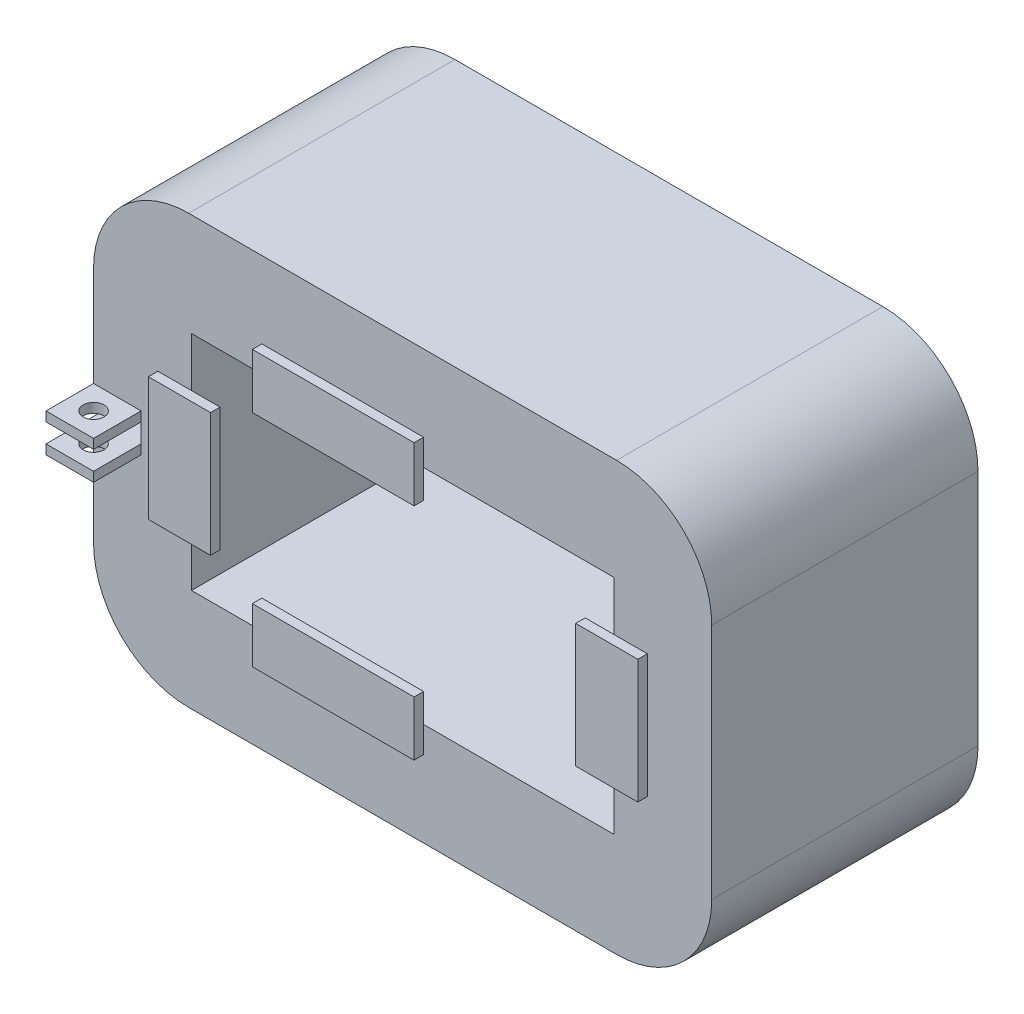
SolidWorks part; units mm, degrees
ref_plane "前基準面" through (0, 0, 0) normal (0, 0, 1) x (1, 0, 0)
ref_plane "上基準面" through (0, 0, 0) normal (0, 1, 0) x (1, 0, 0)
ref_plane "右基準面" through (0, 0, 0) normal (1, 0, 0) x (0, 0, -1)
sketch "草圖1" plane through (0, 0, 0) normal (0, 0, 1) x (1, 0, 0)
  line L0 (-9.02, 0) -> (7.9922, 0) construction
  line L2 (-59.9347, 22.5) -> (5.0653, 22.5)
  line L3 (-59.9347, 22.5) -> (-59.9347, -22.5)
  line L4 (-59.9347, -22.5) -> (5.0653, -22.5)
  line L5 (5.0653, 22.5) -> (5.0653, -22.5)
  dimension "D1" = 45
  dimension "D2" = 22.5
  dimension "D3" = 65
extrude "填料-伸長1" add sketch "草圖1" along normal blind 28
sketch "草圖2" plane through (0, 0, 0) normal (0, 0, 1) x (1, 0, 0)
  line L0 (-59.9347, 0) -> (5.361, 0) construction
  line L1 (-59.9347, 22.5) -> (-59.9347, -22.5) construction
  line L2 (-27.4347, 22.5) -> (-27.4347, -22.5) construction
  line L3 (5.0653, 22.5) -> (-59.9347, 22.5) construction
  line L4 (-59.9347, -22.5) -> (5.0653, -22.5) construction
  line L6 (-49.6347, 11.7) -> (-5.2347, 11.7)
  line L7 (-49.6347, 11.7) -> (-49.6347, -11.7)
  line L8 (-49.6347, -11.7) -> (-5.2347, -11.7)
  line L9 (-5.2347, 11.7) -> (-5.2347, -11.7)
  dimension "D1" = 44.4
  dimension "D2" = 23.4
  dimension "D3" = 10.3
  dimension "D4" = 10.8
extrude "除料-伸長1" cut sketch "草圖2" along normal blind 39
ref_plane "平面1" through (0, 0, 28) normal (0, 0, 1) x (1, 0, 0)
sketch "草圖3" plane through (0, 0, 28) normal (0, 0, 1) x (1, 0, 0)
  line L0 (-59.9347, 22.5) -> (-59.9347, -22.5) construction
  line L2 (-59.9347, 12) -> (-55.9347, 12)
  line L3 (-59.9347, 12) -> (-59.9347, -12)
  line L4 (-59.9347, -12) -> (-55.9347, -12)
  line L5 (-55.9347, 12) -> (-55.9347, -12)
  line L8 (-5.2347, -11.7) -> (-49.6347, -11.7) construction
  dimension "D1" = 4
  dimension "D2" = 24
  dimension "D3" = 0.3
ref_plane "平面2" through (-59.9347, 0, 0) normal (-1, 0, 0) x (0, 0, 1)
sketch "草圖6" plane through (0, 0, 28) normal (0, 0, 1) x (1, 0, 0)
  line L0 (-15.2347, 0.3) -> (5.0653, -22.5)
  line L1 (-5.2347, 11.7) -> (-5.2347, -11.7) construction
  line L2 (-5.2347, -11.7) -> (-49.6347, -11.7) construction
  line L3 (-15.2347, 0.3) -> (-15.2347, -22.5)
  line L4 (-59.9347, -22.5) -> (5.0653, -22.5) construction
  line L5 (-15.2347, -22.5) -> (5.0653, -22.5)
  dimension "D1" = 10
  dimension "D2" = 12
ref_plane "平面4" through (0, 0, 0) normal (0, 0, -1) x (-1, 0, 0)
fillet "圓角1" radius 10 1 edges at (-59.9347, -22.5, 14)
fillet "圓角2" radius 10 1 edges at (-59.9347, 22.5, 14)
fillet "圓角3" radius 10 1 edges at (5.0653, 22.5, 14)
fillet "圓角4" radius 10 1 edges at (5.0653, -22.5, 14)
ref_plane "平面6" through (0, 0, 29) normal (0, 0, 1) x (1, 0, 0)
sketch "草圖10" plane through (0, 0, 29) normal (0, 0, 1) x (1, 0, 0)
  line L6 (-49.6347, 0) -> (-4.2092, 0) construction
  line L7 (-49.6347, -11.7) -> (-49.6347, 11.7) construction
  line L8 (-27.4347, -11.7) -> (-27.4347, 19.297) construction
  line L9 (-5.2347, -11.7) -> (-49.6347, -11.7) construction
  line L11 (-49.6347, 6.5) -> (-53.1651, 6.5)
  line L14 (-53.1651, 6.5) -> (-53.1651, -6.5)
  line L17 (-49.6347, 6.5) -> (-46.6347, 6.5)
  line L18 (-46.6347, 6.5) -> (-46.6347, -6.5)
  line L20 (-42.2347, -11.7) -> (-42.2347, -8.7)
  line L25 (-42.2347, -11.7) -> (-42.2347, -14.4546)
  line L27 (-8.2347, 6.5) -> (-8.2347, -6.5)
  line L28 (-8.2347, -6.5) -> (-5.2347, -6.5)
  line L29 (-5.2347, -6.5) -> (-1.7043, -6.5)
  line L30 (-1.7043, 6.5) -> (-1.7043, -6.5)
  line L32 (-25.2347, 8.7) -> (-25.2347, 14.4546)
  line L33 (-25.2347, -14.4546) -> (-25.2347, -8.7)
  line L34 (-25.2347, -14.4546) -> (-42.2347, -14.4546)
  line L35 (-25.2347, -8.7) -> (-42.2347, -8.7)
  line L36 (-25.2347, 8.7) -> (-42.2347, 8.7)
  line L37 (-25.2347, 14.4546) -> (-42.2347, 14.4546)
  line L38 (-42.2347, 8.7) -> (-42.2347, 14.4546)
  line L39 (-46.6347, -6.5) -> (-53.1651, -6.5)
  line L40 (-1.7043, 6.5) -> (-8.2347, 6.5)
  dimension "D3" = 13
  dimension "D4" = 6.5
extrude "填料-伸長6" add sketch "草圖10" against normal blind 1 separate body
sketch "草圖19" plane through (0, 0, 0) normal (0, 1, 0) x (1, 0, 0)
  line L0 (-59.9347, 13.75) -> (-59.9347, -13.75) construction
  line L1 (-59.9347, 1.0971) -> (-54.9347, 1.0971)
  line L2 (-59.9347, 1.0971) -> (-59.9347, -29)
  line L3 (-59.9347, -29) -> (-54.9347, -29)
  line L4 (-54.9347, 1.0971) -> (-54.9347, -29)
  line L5 (-24.75, -29) -> (24.75, -29) construction
  dimension "D1" = 5
extrude "除料-伸長3" cut sketch "草圖19" against normal blind 1 and the other way blind 1
sketch "草圖20" plane through (0, 0, 0) normal (0, 0, 1) x (1, 0, 0)
  line L0 (-62.8384, 0) -> (-42.2222, 0) construction
  line L1 (-59.9347, 1) -> (-54.9347, 1)
  line L2 (-59.9347, 1) -> (-59.9347, 2)
  line L3 (-59.9347, 2) -> (-54.9347, 2)
  line L4 (-54.9347, 1) -> (-54.9347, 2)
  line L5 (15.95, 0) -> (-15.95, 0) construction
  line L6 (-54.9347, -1) -> (-54.9347, -2)
  line L7 (-59.9347, -2) -> (-54.9347, -2)
  line L8 (-59.9347, -1) -> (-54.9347, -1)
  line L9 (-59.9347, -1) -> (-59.9347, -2)
  dimension "D1" = 5
  dimension "D2" = 1
extrude "填料-伸長12" add sketch "草圖20" against normal blind 5
sketch "草圖21" plane through (0, 0, 28) normal (0, 0, 1) x (1, 0, 0)
  line L0 (-62.4066, 0) -> (-44.8127, 0) construction
  line L1 (-59.9347, 1) -> (-54.9347, 1)
  line L2 (-59.9347, 1) -> (-59.9347, 2)
  line L3 (-59.9347, 2) -> (-54.9347, 2)
  line L4 (-54.9347, 1) -> (-54.9347, 2)
  line L5 (18.7, 0) -> (-18.7, 0) construction
  line L6 (-54.9347, -1) -> (-54.9347, -2)
  line L7 (-59.9347, -1) -> (-54.9347, -1)
  line L8 (-59.9347, -1) -> (-59.9347, -2)
  line L9 (-59.9347, -2) -> (-54.9347, -2)
  dimension "D1" = 1
extrude "填料-伸長13" add sketch "草圖21" along normal blind 5
sketch "草圖22" plane through (0, 0, 0) normal (0, 1, 0) x (1, 0, 0)
  line L0 (-57.4347, 5) -> (-57.4347, -36.775) construction
  line L1 (-54.9347, 5) -> (-59.9347, 5) construction
  line L2 (-54.9347, 2.5) -> (-59.9347, 2.5) construction
  line L3 (-54.9347, 5) -> (-54.9347, 0) construction
  line L4 (-59.9347, 6.325) -> (-59.9347, -6.325) construction
  line L5 (-54.9347, -30.5) -> (-59.9347, -30.5) construction
  line L6 (-54.9347, -33) -> (-54.9347, -28) construction
  circle A0 centre (-57.4347, -30.5) radius 1.1
  circle A1 centre (-57.4347, 2.5) radius 1.1
  dimension "D1" = 2.2
  dimension "D2" = 2.2
extrude "除料-伸長4" cut sketch "草圖22" against normal blind 5 and the other way blind 5
